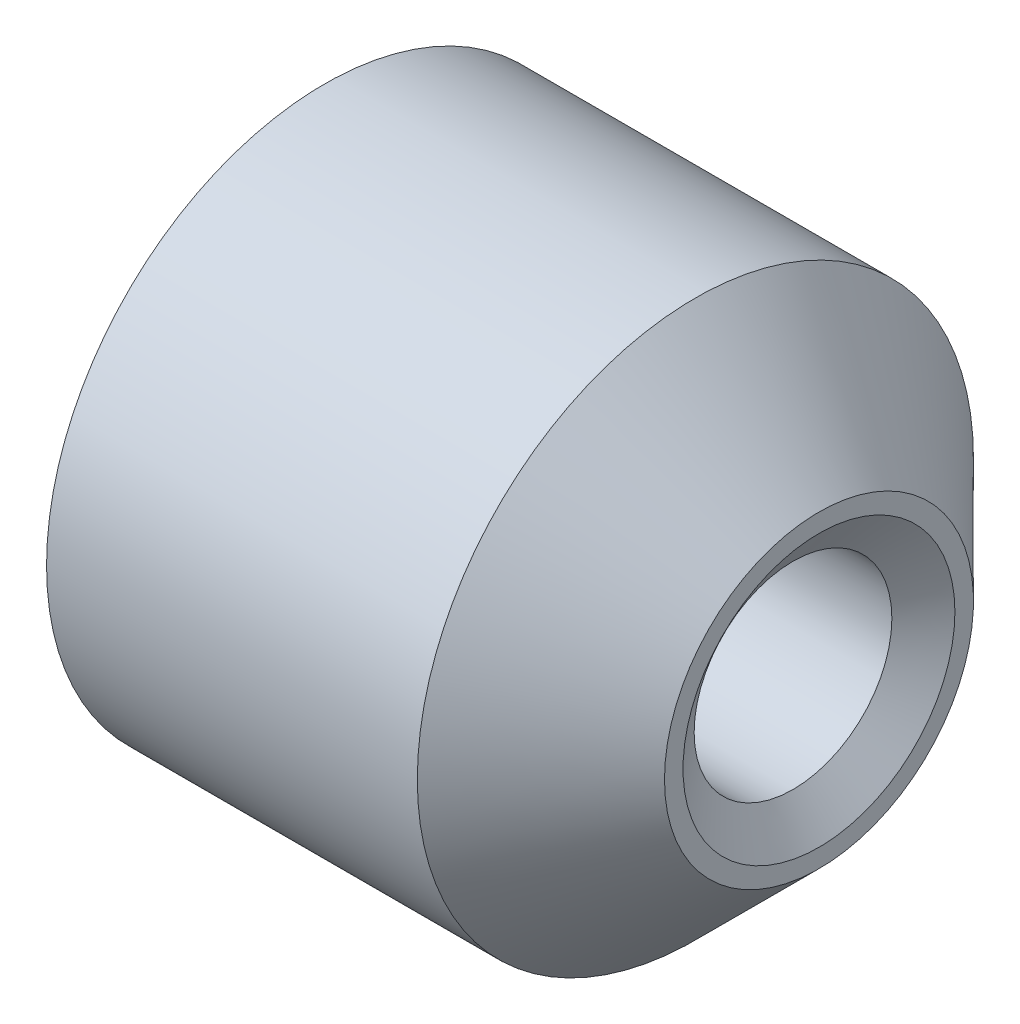
SolidWorks part; units mm, degrees
material "Простая углеродистая сталь"
ref_plane "Спереди" through (0, 0, 0) normal (0, 0, 1) x (1, 0, 0)
ref_plane "Сверху" through (0, 0, 0) normal (0, 1, 0) x (1, 0, 0)
ref_plane "Справа" through (0, 0, 0) normal (1, 0, 0) x (0, 0, -1)
sketch "Эскиз1" plane through (0, 0, 0) normal (0, 0, 1) x (1, 0, 0)
  line L0 (0, 0) -> (11.6839, 0) construction
  line L1 (0, 0.8) -> (0, 2.25)
  line L2 (0, 0.8) -> (4, 0.8)
  line L3 (0, 2.25) -> (3, 2.25)
  line L4 (3, 2.25) -> (4, 1.25)
  line L5 (4, 1.25) -> (4, 0.8)
  dimension "D1" = 4
  dimension "D2" = 4.5
  dimension "D3" = 45
  dimension "D4" = 2.5
  dimension "D5" = 1.6
revolve "Повернуть1" add sketch "Эскиз1" angle 360 about L0
cosmetic thread "Отверстие резьбы1" parameters "D2"=2
hole_wizard "Отверстие обработанное метчиком M2x0.41" positions "Эскиз3" profile "Эскиз2" tap size "M2x0.4" standard "Ansi (метрические)" end condition through all
sketch "Эскиз3" plane through (4, 0, 0) normal (1, 0, 0) x (0, 0, -1)
  point P1 (0, 0)
sketch "Эскиз2" plane through (4, 0, 0) normal (0, 1, 0) x (0, 0, -1)
  line L0 (0, 0) -> (0, 4)
  line L1 (0, 4) -> (1.1, 4)
  line L2 (0.8, 3.7899) -> (0.8, 0.2101)
  line L3 (0.8, 0.2101) -> (1.1, 0)
  line L5 (1.1, 0) -> (0, 0)
  line L6 (-0.8, 0.2101) -> (-1.1, 0) construction
  line L7 (1.1, 4) -> (0.8, 3.7899)
  line L8 (-1.1, 4) -> (-0.8, 3.7899) construction
  line L11 (0, -6.35) -> (0, 107.95) construction
  dimension "Диаметр проходного сверла" = 1.6
  dimension "Глубина проходного сверла" = 4
  dimension "Диаметр передней зенковки" = 2.2
  dimension "Угол передней зенковки" = 110
  dimension "Диаметр задней зенковки" = 2.2
  dimension "Угол задней зенковки" = 110
